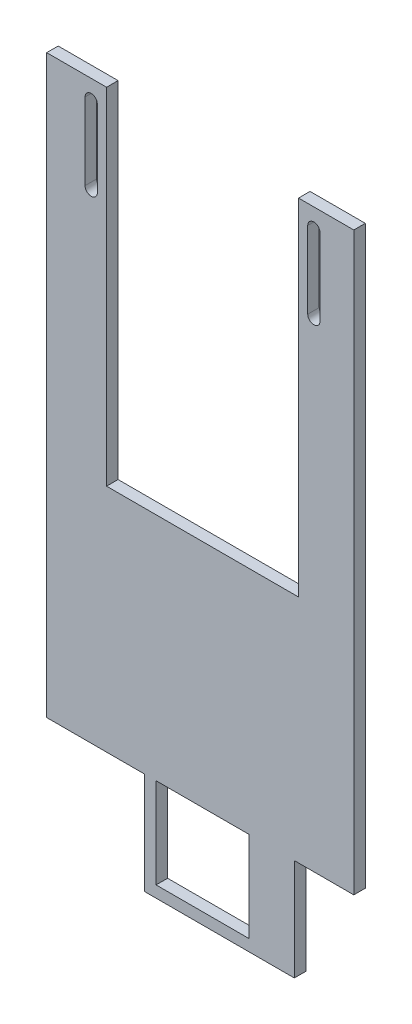
SolidWorks part; units mm, degrees
ref_plane "前视基准面" through (0, 0, 0) normal (0, 0, 1) x (1, 0, 0)
ref_plane "上视基准面" through (0, 0, 0) normal (0, 1, 0) x (1, 0, 0)
ref_plane "右视基准面" through (0, 0, 0) normal (1, 0, 0) x (0, 0, -1)
other "Configuration Table"
sketch "草图1" plane through (0, 0, 0) normal (0, 0, 1) x (1, 0, 0)
  line L0 (9.6507, -72.0326) -> (9.6507, -132.0326) construction
  line L1 (-30.9493, 17.9674) -> (-15.3493, 17.9674)
  line L2 (-30.9493, 17.9674) -> (-30.9493, -132.0326)
  line L3 (-30.9493, -132.0326) -> (-5.4493, -132.0326)
  line L4 (49.0507, 17.9674) -> (49.0507, -132.0326)
  line L5 (-15.3493, 2.9674) -> (-19.3493, 2.9674) construction
  line L6 (-19.3493, 12.9674) -> (-19.3493, -7.0326) construction
  line L7 (-17.7493, 12.9674) -> (-17.7493, -7.0326)
  line L8 (-20.9493, 12.9674) -> (-20.9493, -7.0326)
  line L9 (38.6507, 12.9674) -> (38.6507, -7.0326) construction
  line L10 (37.0507, 12.9674) -> (37.0507, -7.0326)
  line L11 (40.2507, 12.9674) -> (40.2507, -7.0326)
  line L13 (-15.3493, -8.7138) -> (-15.3493, 17.9674)
  line L14 (34.6507, -8.7138) -> (34.6507, 17.9674)
  line L15 (34.6507, 17.9674) -> (49.0507, 17.9674)
  line L16 (-15.3493, -8.7138) -> (-15.3493, -72.0326)
  line L17 (-15.3493, -72.0326) -> (34.6507, -72.0326)
  line L18 (34.6507, -72.0326) -> (34.6507, -8.7138)
  line L19 (-2.4493, -132.0326) -> (21.7507, -132.0326)
  line L20 (33.5507, -132.0326) -> (49.0507, -132.0326)
  line L22 (-5.4493, -132.0326) -> (-5.4493, -158.5326)
  line L23 (-5.4493, -158.5326) -> (33.5507, -158.5326)
  line L24 (33.5507, -158.5326) -> (33.5507, -132.0326)
  line L25 (-2.4493, -132.0326) -> (-2.4493, -155.5326)
  line L26 (-2.4493, -155.5326) -> (21.7507, -155.5326)
  line L27 (21.7507, -155.5326) -> (21.7507, -132.0326)
  arc A0 (-17.7493, 12.9674) -> (-20.9493, 12.9674) centre (-19.3493, 12.9674) ccw
  arc A1 (-20.9493, -7.0326) -> (-17.7493, -7.0326) centre (-19.3493, -7.0326) ccw
  arc A2 (37.0507, 12.9674) -> (40.2507, 12.9674) centre (38.6507, 12.9674) cw
  arc A3 (40.2507, -7.0326) -> (37.0507, -7.0326) centre (38.6507, -7.0326) cw
  point P4 (0, 0)
  point P10 (-19.3493, 2.9674)
  point P17 (38.6507, 2.9674)
  point P26 (9.6507, -8.7138)
  dimension "D4" = 1.6
  dimension "D1" = 80
  dimension "D2" = 150
  dimension "D3" = 10
  dimension "D5" = 20
  dimension "D6" = 15
  dimension "D7" = 25
  dimension "D8" = 60
extrude "凸台-拉伸1" add sketch "草图1" along normal blind 3
